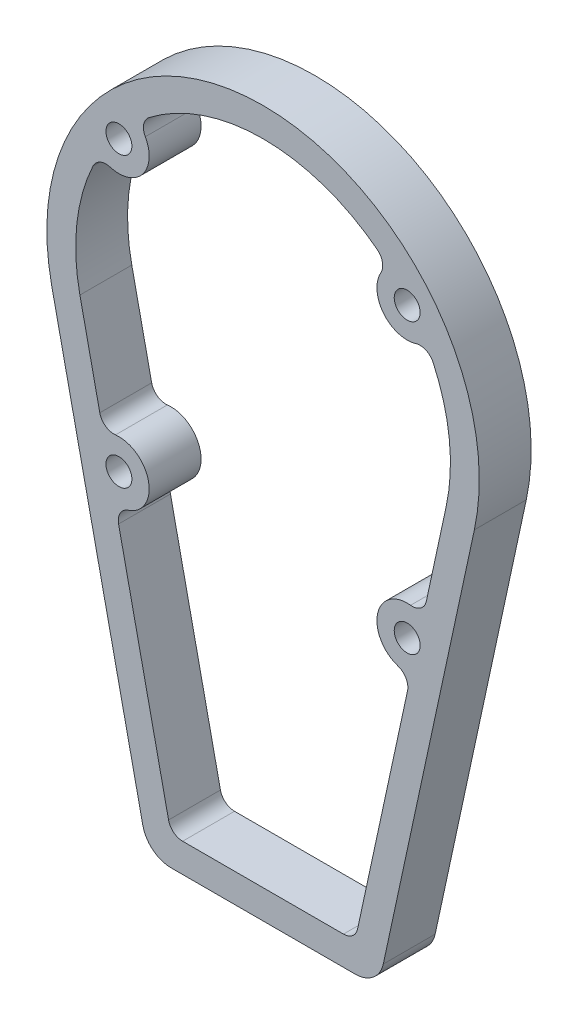
SolidWorks part; units mm, degrees
ref_plane "Front Plane" through (0, 0, 0) normal (0, 0, 1) x (1, 0, 0)
ref_plane "Top Plane" through (0, 0, 0) normal (0, 1, 0) x (1, 0, 0)
ref_plane "Right Plane" through (0, 0, 0) normal (1, 0, 0) x (0, 0, -1)
ref_plane "Plane1" through (0, 0, 18) normal (0, 0, 1) x (1, 0, 0)
sketch "Sketch1" plane through (0, 0, 18) normal (0, 0, 1) x (1, 0, 0)
  line L0 (63.5339, 33.7727) -> (56.6356, 1.8451)
  line L1 (50.1213, -28.305) -> (32.782, -108.5559)
  line L2 (27.8948, -112.5) -> (-27.8948, -112.5)
  line L3 (-32.782, -108.5559) -> (-50.1213, -28.305)
  line L4 (-56.6356, 1.8451) -> (-63.5339, 33.7727)
  line L5 (-73.3084, 31.6608) -> (-41.7043, -114.6119)
  line L6 (-31.9299, -122.5) -> (31.9299, -122.5)
  line L7 (41.7043, -114.6119) -> (73.3084, 31.6608)
  arc A0 (53.0284, 77.4462) -> (59.0098, 74.7553) centre (54.4705, 72.6587) cw
  arc A1 (59.0098, 74.7553) -> (63.5339, 33.7727) centre (0, 47.5) cw
  arc A2 (56.6356, 1.8451) -> (51.1844, -2.067) centre (51.7484, 2.9011) cw
  arc A3 (51.1844, -2.067) -> (46.7714, -22.4913) centre (50, -12.5) ccw
  arc A4 (46.7714, -22.4913) -> (50.1213, -28.305) centre (45.234, -27.2491) cw
  arc A5 (32.782, -108.5559) -> (27.8948, -112.5) centre (27.8948, -107.5) cw
  arc A6 (-27.8948, -112.5) -> (-32.782, -108.5559) centre (-27.8948, -107.5) cw
  arc A7 (-50.1213, -28.305) -> (-46.7714, -22.4913) centre (-45.234, -27.2491) cw
  arc A8 (-46.7714, -22.4913) -> (-51.1844, -2.067) centre (-50, -12.5) ccw
  arc A9 (-51.1844, -2.067) -> (-56.6356, 1.8451) centre (-51.7484, 2.9011) cw
  arc A10 (-63.5339, 33.7727) -> (-59.0098, 74.7553) centre (0, 47.5) cw
  arc A11 (-59.0098, 74.7553) -> (-53.0284, 77.4462) centre (-54.4705, 72.6587) cw
  arc A12 (-53.0284, 77.4462) -> (-40.8562, 92.6615) centre (-50, 87.5) ccw
  arc A13 (-40.8562, 92.6615) -> (-39.5439, 99.0876) centre (-36.502, 95.1194) cw
  arc A14 (-39.5439, 99.0876) -> (39.5439, 99.0876) centre (0, 47.5) cw
  arc A15 (39.5439, 99.0876) -> (40.8562, 92.6615) centre (36.502, 95.1194) cw
  arc A16 (40.8562, 92.6615) -> (53.0284, 77.4462) centre (50, 87.5) ccw
  circle A17 centre (-50, -12.5) radius 4.5
  circle A18 centre (50, 87.5) radius 4.5
  arc A19 (73.3084, 31.6608) -> (-73.3084, 31.6608) centre (0, 47.5) ccw
  arc A20 (-41.7043, -114.6119) -> (-31.9299, -122.5) centre (-31.9299, -112.5) ccw
  arc A21 (31.9299, -122.5) -> (41.7043, -114.6119) centre (31.9299, -112.5) ccw
  circle A22 centre (50, -12.5) radius 4.5
  circle A23 centre (-50, 87.5) radius 4.5
extrude "Boss-Extrude1" add sketch "Sketch1" against normal blind 18
